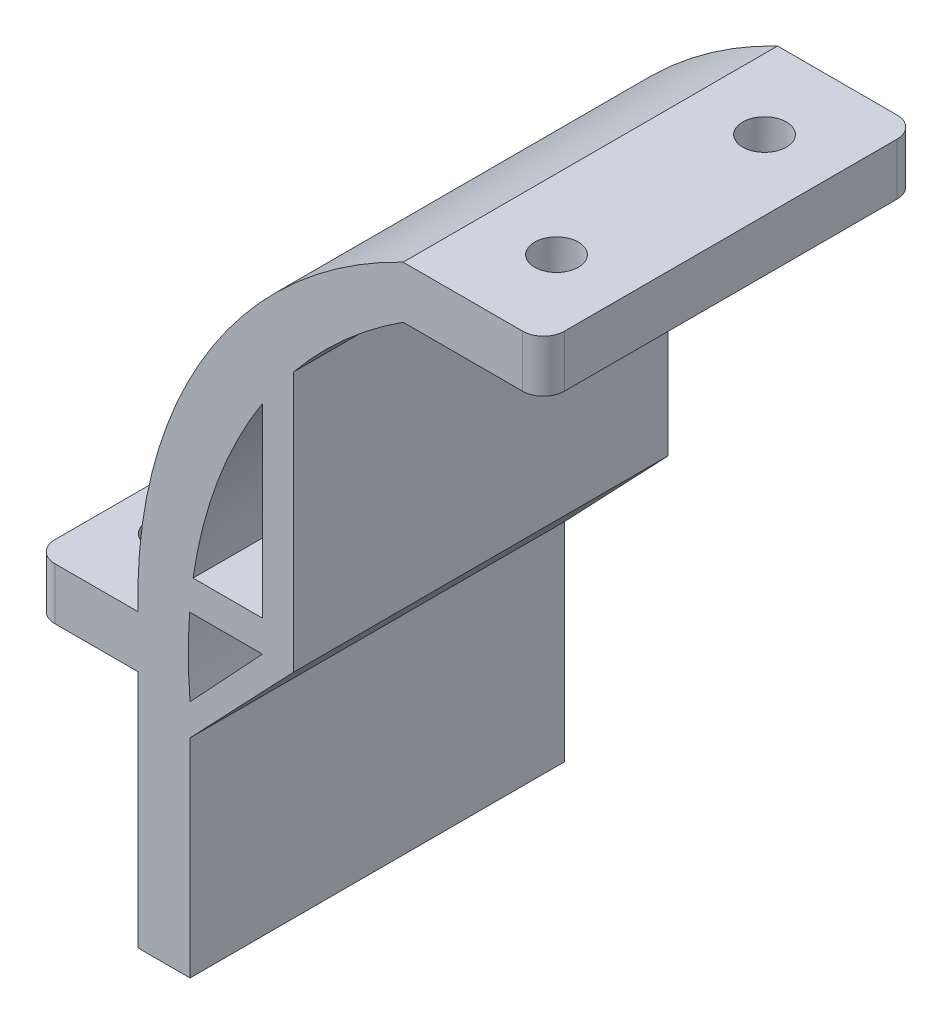
SolidWorks part; units mm, degrees
ref_plane "Front Plane" through (0, 0, 0) normal (0, 0, 1) x (1, 0, 0)
ref_plane "Top Plane" through (0, 0, 0) normal (0, 1, 0) x (1, 0, 0)
ref_plane "Right Plane" through (0, 0, 0) normal (1, 0, 0) x (0, 0, -1)
sketch "Sketch3" plane through (0, 0, 0) normal (0, 0, 1) x (1, 0, 0)
  line L5 (8.4348, 262.2647) -> (-5.0652, 262.2647)
  line L6 (8.4348, 262.2647) -> (8.4348, 257.2647)
  line L7 (8.4348, 257.2647) -> (-5.0652, 257.2647)
  line L8 (-5.0652, 262.2647) -> (-5.0652, 257.2647)
  line L9 (-40.5516, 215.4144) -> (-30.5516, 215.4144)
  line L10 (-40.5516, 215.4144) -> (-40.5516, 220.4144)
  line L11 (-40.5516, 220.4144) -> (-30.5516, 220.4144)
  line L12 (-30.5516, 215.4144) -> (-30.5516, 220.4144)
  line L13 (-30.5516, 215.4144) -> (-25.5516, 215.4144)
  line L14 (-30.5516, 215.4144) -> (-30.5516, 192.4144)
  line L15 (-30.5516, 192.4144) -> (-25.5516, 192.4144)
  line L16 (-25.5516, 215.4144) -> (-25.5516, 192.4144)
  arc A0 (-30.5516, 220.4144) -> (-5.0652, 262.2647) centre (14.4298, 221.7068) cw
  arc A1 (-5.0652, 257.2647) -> (-25.5516, 215.4144) centre (19.2704, 219.4126) ccw
  dimension "D8" = 45
  dimension "D9" = 45
  dimension "D3" = 13.5
  dimension "D4" = 5
  dimension "D6" = 10
  dimension "D7" = 5
extrude "Boss-Extrude1" add sketch "Sketch3" along normal blind 45 contours A1 L8 A0 L12 L13 | L5 L8 L7 L6 | L9 L12 L11 L10 | L16 L13 L14 L15
fillet "Fillet1" radius 2 4 edges at (-40.5516, 217.9144, 0) (-40.5516, 217.9144, 45) (8.4348, 259.7647, 0) (8.4348, 259.7647, 45)
sketch "Sketch5" plane through (0, 262.2647, 0) normal (0, 1, 0) x (1, 0, 0)
  line L0 (-5.0652, -45) -> (-5.0652, 0) construction
  line L2 (6.4348, -45) -> (-5.0652, -45) construction
  circle A0 centre (0.2448, -40) radius 2.1
  circle A2 centre (0.2448, -14.8) radius 2.1
  dimension "D1" = 5.31
  dimension "D2" = 4.2
  dimension "D4" = 5
  dimension "D6" = 4.2
extrude "Cut-Extrude2" cut sketch "Sketch5" against normal blind 45
sketch "Sketch6" plane through (0, 220.4144, 0) normal (0, 1, 0) x (1, 0, 0)
  line L0 (-38.5516, -45) -> (-30.5516, -45) construction
  line L1 (-40.5516, -43) -> (-40.5516, -2) construction
  line L2 (-38.5516, 0) -> (-30.5516, 0) construction
  circle A0 centre (-35.5516, -10) radius 2.1
  circle A1 centre (-35.5516, -35) radius 2.1
  dimension "D1" = 4.2
  dimension "D2" = 4.2
  dimension "D3" = 10
  dimension "D4" = 5
  dimension "D5" = 5
  dimension "D6" = 10
extrude "Cut-Extrude3" cut sketch "Sketch6" against normal blind 45
sketch "Sketch7" plane through (0, 262.2647, 0) normal (0, 1, 0) x (1, 0, 0)
  line L1 (-3.0108, -10.6298) -> (5.1997, -10.6298)
  line L2 (-3.0108, -10.6298) -> (-3.0108, -43.2171)
  line L3 (-3.0108, -43.2171) -> (5.1997, -43.2171)
  line L4 (5.1997, -10.6298) -> (5.1997, -43.2171)
extrude "Boss-Extrude2" add sketch "Sketch7" against normal up to surface (5 mm away) contours L2 L1 L4 L3 up to face at (0.2448, 257.2647, 37.9)
sketch "Sketch8" plane through (0, 262.2647, 0) normal (0, 1, 0) x (1, 0, 0)
  line L0 (-5.0652, -35.2) -> (8.4348, -35.2)
  line L1 (-5.0652, -45) -> (-5.0652, 0) construction
  line L2 (8.4348, -43) -> (8.4348, -2) construction
  line L3 (6.4348, 0) -> (-5.0652, 0) construction
  circle A0 centre (0.2448, -5) radius 2.1
  circle A1 centre (0.2448, -30.2) radius 2.1
  dimension "D1" = 4.2
  dimension "D2" = 4.2
  dimension "D3" = 5
  dimension "D4" = 5
  dimension "D6" = 5.31
  dimension "D7" = 5.31
  dimension "D5" = 35.2
extrude "Cut-Extrude5" cut sketch "Sketch8" against normal blind 45 contours A0 | A1
sketch "Sketch9" plane through (0, 0, 45) normal (0, 0, 1) x (1, 0, 0)
  line L0 (-25.5974, 222.8598) -> (-15.5974, 222.8598)
  line L1 (-15.5974, 222.8598) -> (-15.5974, 247.8598)
  line L2 (-18.5974, 243.7238) -> (-18.5974, 225.8598)
  line L3 (-18.5974, 225.8598) -> (-25.2654, 225.8598)
  line L4 (-15.5974, 222.8598) -> (-25.5516, 212.4144)
  line L5 (-25.5516, 215.4144) -> (-25.5516, 192.4144) construction
  line L6 (-18.5974, 222.8598) -> (-25.5516, 215.4144)
  arc A0 (-5.0652, 257.2647) -> (-25.5516, 215.4144) centre (19.2704, 219.4126) ccw construction
  point P8 (-20.5974, 222.8598)
  line M11 (-25.5516, 192.4144) -> (-25.5516, 215.4144)
  arc M12 (-25.5516, 215.4144) -> (-5.0652, 257.2647) centre (19.2704, 219.4126) cw
  dimension "D1" = 25
  dimension "D2" = 10
  dimension "D3" = 3
  dimension "D4" = 3
  dimension "D5" = 3
extrude "Boss-Extrude3" add sketch "Sketch9" against normal through all contours L2 L3 L0 L1 M12 | L0 L6 L4 M11
sketch "Sketch10" plane through (0, 0, 45) normal (0, 0, 1) x (1, 0, 0)
  line L1 (8.4348, 262.2647) -> (-51.9209, 262.2647)
  line L2 (8.4348, 262.2647) -> (8.4348, 186.8831)
  line L3 (8.4348, 186.8831) -> (-51.9209, 186.8831)
  line L4 (-51.9209, 262.2647) -> (-51.9209, 186.8831)
extrude "Cut-Extrude7" cut sketch "Sketch10" against normal blind 9
sketch "Sketch13" plane through (0, 220.4144, 0) normal (0, 1, 0) x (1, 0, 0)
  line L0 (-30.5516, -36) -> (-33.705, -36) construction
  line L1 (-38.2234, -6.9443) -> (-32.1283, -6.9443)
  line L2 (-38.2234, -6.9443) -> (-38.2234, -36)
  line L3 (-38.2234, -36) -> (-32.1283, -36)
  line L4 (-32.1283, -6.9443) -> (-32.1283, -36)
extrude "Boss-Extrude6" add sketch "Sketch13" against normal up to surface (5 mm away) up to face at (-35.5516, 215.4144, 12.1)
sketch "Sketch14" plane through (0, 262.2647, 0) normal (0, 1, 0) x (1, 0, 0)
  line L1 (-3.0485, -2.0187) -> (3.3761, -2.0187)
  line L2 (-3.0485, -2.0187) -> (-3.0485, -32.8034)
  line L3 (-3.0485, -32.8034) -> (3.3761, -32.8034)
  line L4 (3.3761, -2.0187) -> (3.3761, -32.8034)
extrude "Boss-Extrude7" add sketch "Sketch14" against normal up to surface (5 mm away) up to face at (2.7176, 257.2647, 14.7172)
fillet "Fillet3" radius 2 2 edges at (-40.5516, 217.9144, 36) (8.4348, 259.7647, 36)
sketch "Sketch15" plane through (0, 220.4144, 0) normal (0, 1, 0) x (1, 0, 0)
  line L0 (-38.5516, 0) -> (-30.5516, 0) construction
  line L1 (-40.5516, -34) -> (-40.5516, -2) construction
  line L2 (-30.5516, -36) -> (-38.5516, -36) construction
  circle A0 centre (-35.5516, -8) radius 2.1
  circle A1 centre (-35.5516, -28) radius 2.1
  dimension "D1" = 4.2
  dimension "D2" = 4.2
  dimension "D3" = 8
  dimension "D4" = 5
  dimension "D5" = 5
  dimension "D6" = 8
extrude "Cut-Extrude8" cut sketch "Sketch15" against normal blind 9
sketch "Sketch16" plane through (0, 262.2647, 0) normal (0, 1, 0) x (1, 0, 0)
  line L5 (1.6848, 0) -> (1.6848, -10.1) construction
  line L6 (1.6848, -25.9) -> (1.6848, -30.1) construction
  circle A0 centre (1.6848, -8) radius 2.1
  circle A1 centre (1.6848, -28) radius 2.1
  dimension "D2" = 4.2
  dimension "D3" = 4.2
extrude "Cut-Extrude9" cut sketch "Sketch16" against normal blind 9
